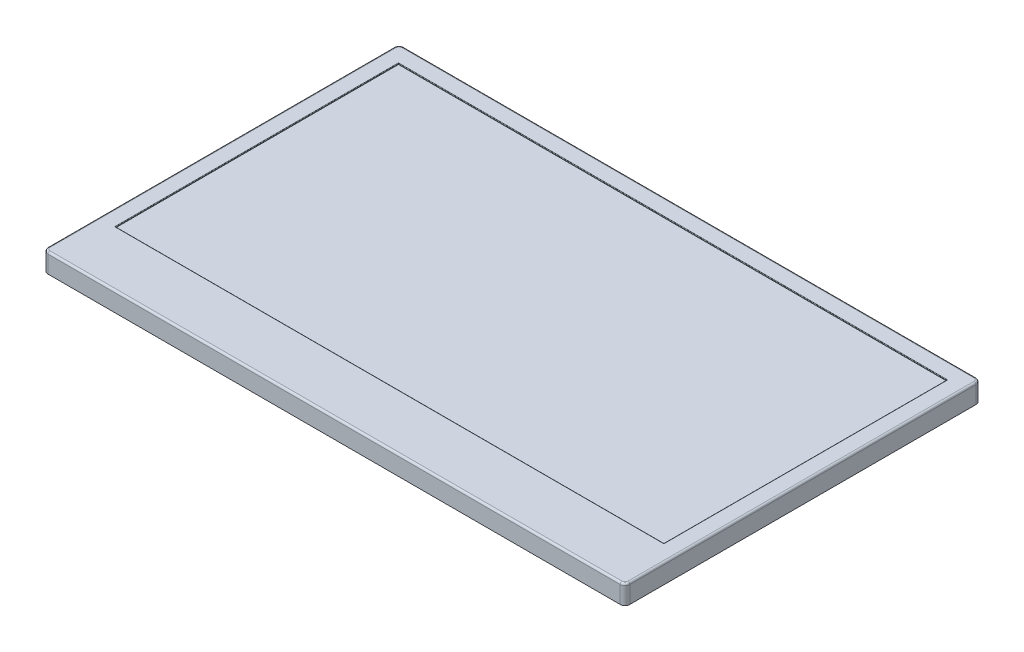
SolidWorks part; units mm, degrees
ref_plane "Front Plane" through (0, 0, 0) normal (0, 0, 1) x (1, 0, 0)
ref_plane "Top Plane" through (0, 0, 0) normal (0, 1, 0) x (1, 0, 0)
ref_plane "Right Plane" through (0, 0, 0) normal (1, 0, 0) x (0, 0, -1)
sketch "Sketch1" plane through (0, 0, 0) normal (0, 1, 0) x (1, 0, 0)
  line L1 (0, 0) -> (60.5, 0)
  line L2 (0, 0) -> (0, 37)
  line L3 (0, 37) -> (60.5, 37)
  line L4 (60.5, 0) -> (60.5, 37)
  dimension "D1" = 60.5
  dimension "D2" = 37
extrude "Boss-Extrude1" add sketch "Sketch1" along normal blind 2 contours L3 L4 L1 L2
sketch "Sketch2" plane through (0, 2, 0) normal (0, 1, 0) x (1, 0, 0)
  line L0 (30.25, 35.2) -> (30.25, 37) construction
  line L1 (1.745, 35.2) -> (58.755, 35.2)
  line L2 (1.745, 35.2) -> (1.745, 5.79)
  line L3 (1.745, 5.79) -> (58.755, 5.79)
  line L4 (58.755, 35.2) -> (58.755, 5.79)
  line L5 (0, 37) -> (60.5, 37) construction
  line L6 (1.745, 20.495) -> (0, 20.495) construction
  line L8 (58.755, 20.495) -> (60.5, 20.495) construction
  dimension "D1" = 29.41
  dimension "D2" = 57.01
  dimension "D3" = 1.8
extrude "Cut-Extrude1" cut sketch "Sketch2" against normal blind 0.1
fillet "Fillet1" radius 0.5 4 edges at (0, 1, 0) (60.5, 1, 0) (60.5, 1, -37) (0, 1, -37)
fillet "Fillet2" radius 0.2 8 edges at (0.1464, 2, -0.1464) (30.25, 2, 0) (60.3536, 2, -0.1464) (60.5, 2, -18.5) (60.3536, 2, -36.8536) (30.25, 2, -37) (0.1464, 2, -36.8536) (0, 2, -18.5)
fillet "Fillet3" radius 0.05 4 edges at (30.25, 2, -5.79) (58.755, 2, -20.495) (30.25, 2, -35.2) (1.745, 2, -20.495)
